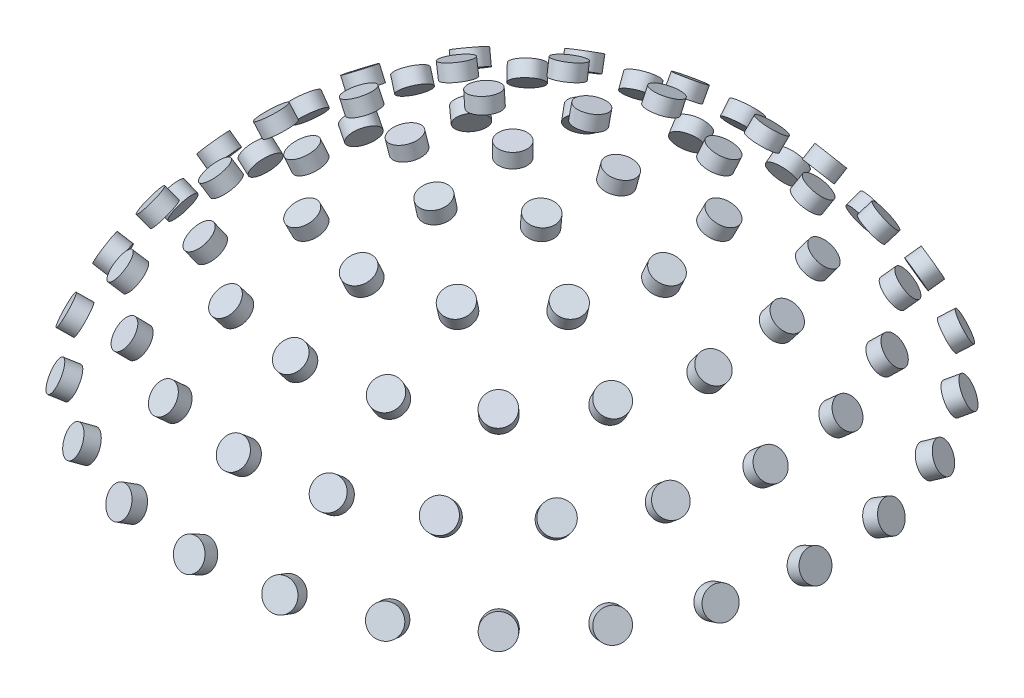
SolidWorks part; units mm, degrees
ref_plane "Front Plane" through (0, 0, 0) normal (0, 0, 1) x (1, 0, 0)
ref_plane "Top Plane" through (0, 0, 0) normal (0, 1, 0) x (1, 0, 0)
ref_plane "Right Plane" through (0, 0, 0) normal (1, 0, 0) x (0, 0, -1)
sketch "Sketch1" plane through (0, 0, 0) normal (0, 0, 1) x (1, 0, 0)
  line L0 (0, 0) -> (12, 0)
  line L1 (0, 0) -> (0, 12)
  arc A0 (0, 12) -> (12, 0) centre (0, 0) cw
  dimension "D1" = 12
  dimension "D2" = 12
ref_plane "Plane1" through (0, 12.2, 0) normal (0, 1, 0) x (1, 0, 0)
sketch "Sketch2" plane through (0, 12.2, 0) normal (0, 1, 0) x (1, 0, 0)
  circle A0 centre (0, 0) radius 0.5
  dimension "D1" = 1
extrude "Boss-Extrude1" add sketch "Sketch2" along normal blind 0.5 contours A0
pattern_circular "CirPattern1" count 2 every 12.5 about axis through (0, 0, 0) along (1, 0, 0) of "Boss-Extrude1"
pattern_circular "CirPattern2" count 2 every 25 about axis through (0, 0, 0) along (1, 0, 0) of bodies 101
pattern_circular "CirPattern3" count 2 every 37.5 about axis through (0, 0, 0) along (1, 0, 0) of bodies 101
pattern_circular "CirPattern4" count 2 every 50 about axis through (0, 0, 0) along (1, 0, 0) of bodies 101
pattern_circular "CirPattern5" count 2 every 62.5 about axis through (0, 0, 0) along (1, 0, 0) of bodies 101
pattern_circular "CirPattern6" count 6 over 360 about axis through (0, 0, 0) along (0, 1, 0) of bodies 102
pattern_circular "CirPattern7" count 12 over 360 about axis through (0, 0, 0) along (0, 1, 0) of bodies 103
pattern_circular "CirPattern8" count 17 over 360 about axis through (0, 0, 0) along (0, 1, 0) of bodies 104
pattern_circular "CirPattern9" count 21 over 360 about axis through (0, 0, 0) along (0, 1, 0) of bodies 105
pattern_circular "CirPattern10" count 25 over 360 about axis through (0, 0, 0) along (0, 1, 0) of bodies 106
sketch "Sketch3" plane through (0, 0, 0) normal (0, 1, 0) x (1, 0, 0)
  circle A0 centre (0, 0) radius 10.5
  dimension "D1" = 21
equation "\"D1@Sketch1\" = \"dia_outer_in\""
equation "\"D2@Sketch1\" = \"dia_outer_in\""
equation "\"D1@Sketch2\"=\"d_marker\""
equation "\"D1@Boss-Extrude1\"=\"t_marker\""
equation "\"D2@CirPattern1\"=\"degrees\""
equation "\"D2@CirPattern2\"=2*\"degrees\""
equation "\"D2@CirPattern3\"=3*\"degrees\""
equation "\"D2@CirPattern4\"=4*\"degrees\""
equation "\"D2@CirPattern5\"=5*\"degrees\""
equation "\"D1@CirPattern6\" = \"n_markers_1\""
equation "\"D1@CirPattern7\" = \"n_markers_2\""
equation "\"D1@CirPattern8\" = \"n_markers_3\""
equation "\"D1@CirPattern9\"= \"n_markers_4\""
equation "\"D1@CirPattern10\" = \"n_markers_5\""
equation "\"dia_difflayer\"= 13"
equation "\"dia_outer_out\"= 12.5"
equation "\"dia_outer_in\"= 12"
equation "\"dia_inner_out\"= 11"
equation "\"dia_inner_in\"= 10.5"
equation "\"degrees\"= 12.5"
equation "\"d_marker\"= 1"
equation "\"t_marker\"= 0.5"
equation "\"n_markers_1\"= 6"
equation "\"n_markers_2\"= round ( 6 * sin ( 2*\"degrees\" ) / sin ( \"degrees\" ) )"
equation "\"n_markers_3\"= round ( 6 * sin ( 3*\"degrees\" ) / sin ( \"degrees\" ) )"
equation "\"n_markers_4\"= round ( 6 * sin ( 4*\"degrees\" ) / sin ( \"degrees\" ) )"
equation "\"n_markers_5\"= round ( 6 * sin ( 5*\"degrees\" ) / sin ( \"degrees\" ) )"
equation "\"n_teeth\"= 8"
equation "\"tolerance_domes\"= 0.4"
equation "\"tolerance_large\"= 0.4"
equation "\"pinhole_slot\"= 3.8"
equation "\"D1@Plane1\"=\"dia_outer_in\"+\"tolerance_domes\"/2"
